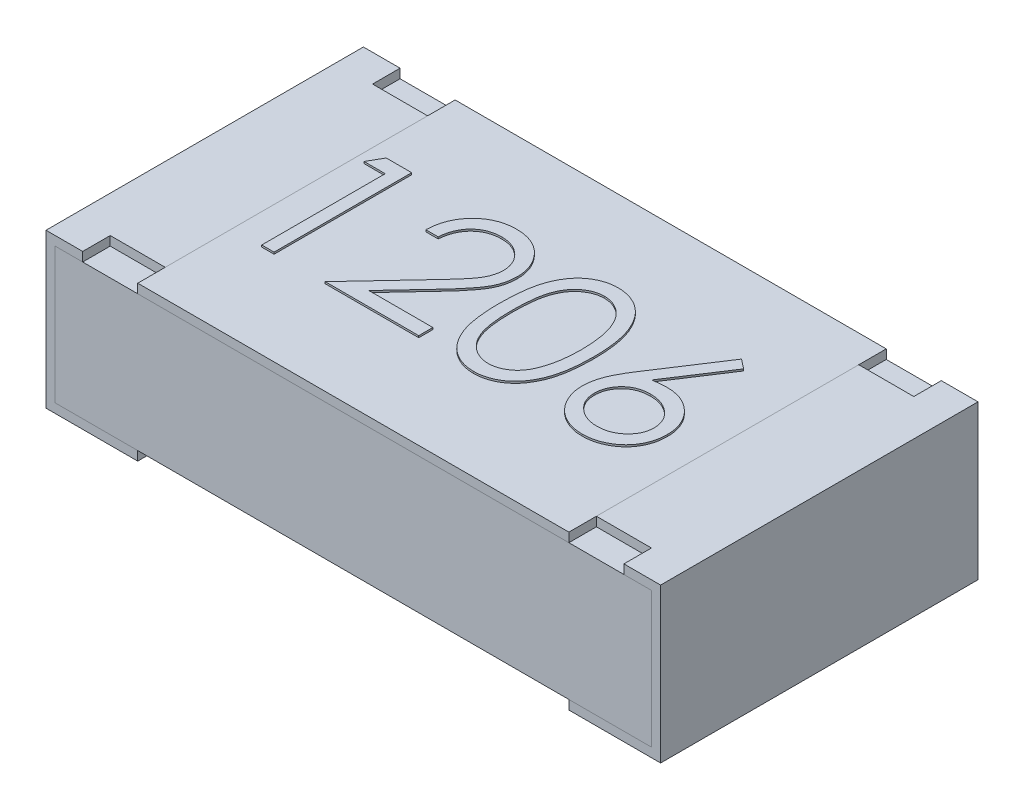
SolidWorks part; units mm, degrees
ref_plane "Alzado" through (0, 0, 0) normal (0, 0, 1) x (1, 0, 0)
ref_plane "Planta" through (0, 0, 0) normal (0, 1, 0) x (1, 0, 0)
ref_plane "Vista lateral" through (0, 0, 0) normal (1, 0, 0) x (0, 0, -1)
sketch "Croquis1" plane through (0, 0, 0) normal (0, 1, 0) x (1, 0, 0)
  line L1 (1.625, 0.865) -> (-1.625, 0.865)
  line L2 (1.625, 0.865) -> (1.625, -0.865)
  line L3 (1.625, -0.865) -> (-1.625, -0.865)
  line L4 (-1.625, 0.865) -> (-1.625, -0.865)
  line L5 (1.625, 0.865) -> (-1.625, -0.865) construction
  line L6 (1.625, -0.865) -> (-1.625, 0.865) construction
  point P0 (0, 0)
  dimension "D1" = 1.73
  dimension "D2" = 3.25
extrude "Extruir1" add sketch "Croquis1" along normal blind 0.79
sketch "Croquis2" plane through (0, 0, 0.865) normal (0, 0, 1) x (1, 0, 0)
  line L0 (1.625, 0.79) -> (1.625, 0) construction
  line L1 (-1.625, 0) -> (1.625, 0)
  line L2 (-1.625, 0) -> (-1.625, 0.05)
  line L3 (-1.625, 0.05) -> (1.625, 0.05)
  line L4 (1.625, 0) -> (1.625, 0.05)
  dimension "D1" = 0.05
extrude "Extruir2" cut sketch "Croquis2" against normal through all
sketch "Croquis3" plane through (0, 0, 0.865) normal (0, 0, 1) x (1, 0, 0)
  line L0 (-1.175, 0.84) -> (-1.675, 0.84)
  line L1 (-1.675, 0.84) -> (-1.675, 0)
  line L2 (-1.675, 0) -> (-1.175, 0)
  line L4 (-1.625, 0.79) -> (-1.625, 0.05) construction
  line L5 (-1.625, 0.79) -> (1.625, 0.79) construction
  dimension "D1" = 0.05
  dimension "D2" = 0.05
  dimension "D3" = 0.5
  dimension "D4" = 0.5
  dimension "D5" = 0.84
sketch3d "Croquis3D1"
  line L0 (-1.175, 0.84, 0.865) -> (-1.175, 0.84, -0.865)
  line L1 (-1.175, 0.84, -0.865) -> (-1.175, 0.79, -0.865)
  line L2 (-1.175, 0.79, -0.865) -> (-1.175, 0.79, 0.865)
  line L3 (-1.175, 0.79, 0.865) -> (-1.175, 0.84, 0.865)
  line L4 (-1.625, 0.79, -0.865) -> (-1.625, 0.79, 0.865) construction
sweep "Barrer1" add profiles "Croquis3D1" path "Croquis3"
ref_plane "Plano1" through (0, 0.79, 0.865) normal (1, 0, 0) x (0, 0, -1)
mirror "Simetría1" about plane through (0, 0.79, 0.865) normal (1, 0, 0) of bodies 104
sketch "Croquis4" plane through (-1.175, 0, 0) normal (1, 0, 0) x (0, 0, -1)
  line L1 (-0.865, 0.84) -> (0.865, 0.84)
  line L2 (-0.865, 0.84) -> (-0.865, 0.79)
  line L3 (-0.865, 0.79) -> (0.865, 0.79)
  line L4 (0.865, 0.84) -> (0.865, 0.79)
extrude "Extruir3" add sketch "Croquis4" along normal up to surface (2.35 mm away) separate body up to face at (1.175, 0.815, 0)
sketch "Croquis5" plane through (0, 0.84, 0) normal (0, 1, 0) x (1, 0, 0)
  line L0 (0, -0.865) -> (0, 0.865) construction
  line L1 (-1.175, -0.865) -> (-1.475, -0.865)
  line L2 (-1.175, -0.865) -> (-1.175, -0.715)
  line L3 (-1.175, -0.715) -> (-1.475, -0.715)
  line L4 (-1.475, -0.865) -> (-1.475, -0.715)
  line L5 (1.175, -0.865) -> (-1.175, -0.865) construction
  line L6 (1.175, 0.865) -> (-1.175, 0.865) construction
  line L7 (-1.175, 0) -> (1.175, 0) construction
  line L8 (-1.175, 0.865) -> (-1.175, -0.865) construction
  line L9 (1.175, 0.865) -> (1.175, -0.865) construction
  line L10 (-1.475, 0.865) -> (-1.475, 0.715)
  line L11 (-1.175, 0.715) -> (-1.475, 0.715)
  line L12 (-1.175, 0.865) -> (-1.175, 0.715)
  line L13 (-1.175, 0.865) -> (-1.475, 0.865)
  line L14 (1.175, 0.865) -> (1.475, 0.865)
  line L15 (1.175, 0.865) -> (1.175, 0.715)
  line L16 (1.175, 0.715) -> (1.475, 0.715)
  line L17 (1.475, 0.865) -> (1.475, 0.715)
  line L18 (1.475, -0.865) -> (1.475, -0.715)
  line L19 (1.175, -0.715) -> (1.475, -0.715)
  line L20 (1.175, -0.865) -> (1.175, -0.715)
  line L21 (1.175, -0.865) -> (1.475, -0.865)
  dimension "D1" = 0.15
  dimension "D2" = 0.3
extrude "Extruir4" cut sketch "Croquis5" against normal up to next (0.05 mm away)
sketch "Sketch1" plane through (0, 0.84, 0) normal (0, 1, 0) x (1, 0, 0)
  text T0 "1206" font "Century Gothic" height 0.75
extrude "Boss-Extrude1" add sketch "Sketch1" along normal blind 0.01
